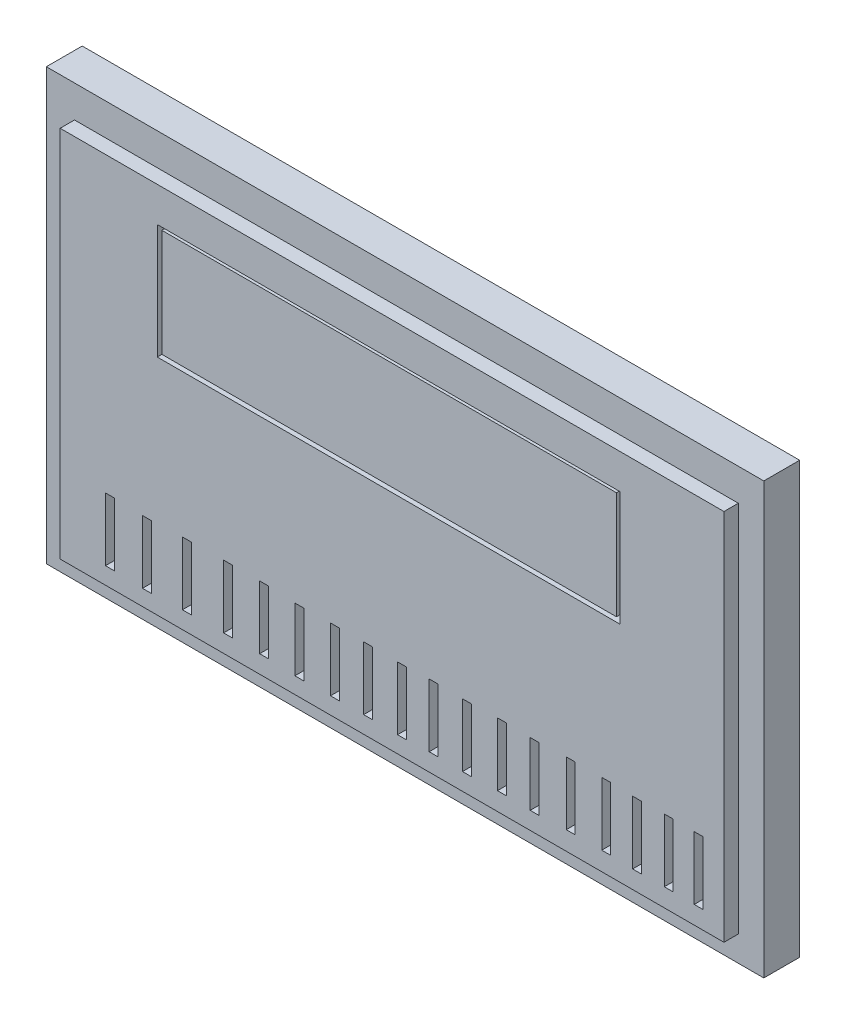
SolidWorks part; units mm, degrees
material "ABS PC"
ref_plane "Front Plane" through (0, 0, 0) normal (0, 0, 1) x (1, 0, 0)
ref_plane "Top Plane" through (0, 0, 0) normal (0, 1, 0) x (1, 0, 0)
ref_plane "Right Plane" through (0, 0, 0) normal (1, 0, 0) x (0, 0, -1)
sketch "Sketch2" plane through (0, 0, 0) normal (0, 0, 1) x (1, 0, 0)
  line L1 (-29.7872, 22.9787) -> (70.2128, 22.9787)
  line L2 (-29.7872, 22.9787) -> (-29.7872, -37.0213)
  line L3 (-29.7872, -37.0213) -> (70.2128, -37.0213)
  line L4 (70.2128, 22.9787) -> (70.2128, -37.0213)
  dimension "D1" = 100
  dimension "D2" = 60
extrude "Boss-Extrude1" add sketch "Sketch2" along normal blind 5
sketch "Sketch3" plane through (0, 0, 5) normal (0, 0, 1) x (1, 0, 0)
  line L1 (-25.8599, 18.5127) -> (66.6601, 18.5127)
  line L2 (-25.8599, 18.5127) -> (-25.8599, -33.4873)
  line L3 (-25.8599, -33.4873) -> (66.6601, -33.4873)
  line L4 (66.6601, 18.5127) -> (66.6601, -33.4873)
  dimension "D1" = 92.52
  dimension "D2" = 52
extrude "Boss-Extrude2" add sketch "Sketch3" along normal blind 2
sketch "Sketch4" plane through (0, 0, 0) normal (0, 0, -1) x (-1, 0, 0)
  line L1 (-52.1735, 13.6653) -> (12.3265, 13.6653)
  line L2 (-52.1735, 13.6653) -> (-52.1735, -2.3347)
  line L3 (-52.1735, -2.3347) -> (12.3265, -2.3347)
  line L4 (12.3265, 13.6653) -> (12.3265, -2.3347)
  dimension "D1" = 16
  dimension "D2" = 64.5
extrude "Cut-Extrude1" cut sketch "Sketch4" against normal blind 14
sketch "Sketch5" plane through (0, 0, 0) normal (0, 0, -1) x (-1, 0, 0)
  line L0 (-59.5883, -22.1519) -> (-58.3471, -22.1519)
  line L1 (-63.758, -22.1977) -> (-62.5168, -22.1977)
  line L2 (-63.758, -22.1977) -> (-63.758, -30.9895)
  line L3 (-63.758, -30.9895) -> (-62.5168, -30.9895)
  line L4 (-62.5168, -22.1977) -> (-62.5168, -30.9895)
  line L5 (-59.5883, -22.1519) -> (-59.5883, -30.9437)
  line L6 (-59.5883, -30.9437) -> (-58.3471, -30.9437)
  line L7 (-58.3471, -22.1519) -> (-58.3471, -30.9437)
  line L8 (-55.1704, -22.2108) -> (-53.9292, -22.2108)
  line L9 (-55.1704, -22.2108) -> (-55.1704, -31.0026)
  line L10 (-55.1704, -31.0026) -> (-53.9292, -31.0026)
  line L11 (-53.9292, -22.2108) -> (-53.9292, -31.0026)
  line L16 (-50.8703, -22.093) -> (-49.6291, -22.093)
  line L17 (-50.8703, -22.093) -> (-50.8703, -30.8848)
  line L18 (-50.8703, -30.8848) -> (-49.6291, -30.8848)
  line L19 (-49.6291, -22.093) -> (-49.6291, -30.8848)
  line L20 (-45.9223, -22.093) -> (-44.6811, -22.093)
  line L21 (-45.9223, -22.093) -> (-45.9223, -30.8848)
  line L22 (-45.9223, -30.8848) -> (-44.6811, -30.8848)
  line L23 (-44.6811, -22.093) -> (-44.6811, -30.8848)
  line L24 (-40.8963, -22.2716) -> (-39.6551, -22.2716)
  line L25 (-40.8963, -22.2716) -> (-40.8963, -31.0634)
  line L26 (-40.8963, -31.0634) -> (-39.6551, -31.0634)
  line L27 (-39.6551, -22.2716) -> (-39.6551, -31.0634)
  line L28 (-36.3326, -22.1765) -> (-35.0914, -22.1765)
  line L29 (-36.3326, -22.1765) -> (-36.3326, -30.9683)
  line L30 (-36.3326, -30.9683) -> (-35.0914, -30.9683)
  line L31 (-35.0914, -22.1765) -> (-35.0914, -30.9683)
  line L32 (-31.4565, -22.3097) -> (-30.2153, -22.3097)
  line L33 (-31.4565, -22.3097) -> (-31.4565, -31.1015)
  line L34 (-31.4565, -31.1015) -> (-30.2153, -31.1015)
  line L35 (-30.2153, -22.3097) -> (-30.2153, -31.1015)
  line L36 (-26.8145, -22.2395) -> (-25.5733, -22.2395)
  line L37 (-26.8145, -22.2395) -> (-26.8145, -31.0313)
  line L38 (-26.8145, -31.0313) -> (-25.5733, -31.0313)
  line L39 (-25.5733, -22.2395) -> (-25.5733, -31.0313)
  line L40 (-22.4079, -22.3852) -> (-21.1667, -22.3852)
  line L41 (-22.4079, -22.3852) -> (-22.4079, -31.177)
  line L42 (-22.4079, -31.177) -> (-21.1667, -31.177)
  line L43 (-21.1667, -22.3852) -> (-21.1667, -31.177)
  line L44 (-17.682, -22.325) -> (-16.4408, -22.325)
  line L45 (-17.682, -22.325) -> (-17.682, -31.1168)
  line L46 (-17.682, -31.1168) -> (-16.4408, -31.1168)
  line L47 (-16.4408, -22.325) -> (-16.4408, -31.1168)
  line L48 (-13.0637, -22.36) -> (-11.8225, -22.36)
  line L49 (-13.0637, -22.36) -> (-13.0637, -31.1518)
  line L50 (-13.0637, -31.1518) -> (-11.8225, -31.1518)
  line L51 (-11.8225, -22.36) -> (-11.8225, -31.1518)
  line L52 (-8.0956, -22.43) -> (-6.8544, -22.43)
  line L53 (-8.0956, -22.43) -> (-8.0956, -31.2218)
  line L54 (-8.0956, -31.2218) -> (-6.8544, -31.2218)
  line L55 (-6.8544, -22.43) -> (-6.8544, -31.2218)
  line L56 (-3.1883, -22.2201) -> (-1.9471, -22.2201)
  line L57 (-3.1883, -22.2201) -> (-3.1883, -31.0119)
  line L58 (-3.1883, -31.0119) -> (-1.9471, -31.0119)
  line L59 (-1.9471, -22.2201) -> (-1.9471, -31.0119)
  line L60 (1.8406, -22.2201) -> (3.0818, -22.2201)
  line L61 (1.8406, -22.2201) -> (1.8406, -31.0119)
  line L62 (1.8406, -31.0119) -> (3.0818, -31.0119)
  line L63 (3.0818, -22.2201) -> (3.0818, -31.0119)
  line L64 (7.5795, -22.2992) -> (8.8207, -22.2992)
  line L65 (7.5795, -22.2992) -> (7.5795, -31.091)
  line L66 (7.5795, -31.091) -> (8.8207, -31.091)
  line L67 (8.8207, -22.2992) -> (8.8207, -31.091)
extrude "Cut-Extrude2" cut sketch "Sketch5" against normal blind 14
sketch "Sketch6" plane through (0, 0, 0) normal (0, 0, -1) x (-1, 0, 0)
  line L0 (13.147, -22.4941) -> (14.3882, -22.4941)
  line L1 (13.147, -22.4941) -> (13.147, -31.2859)
  line L2 (13.147, -31.2859) -> (14.3882, -31.2859)
  line L3 (14.3882, -22.4941) -> (14.3882, -31.2859)
  line L8 (18.3076, -22.3422) -> (19.5488, -22.3422)
  line L9 (18.3076, -22.3422) -> (18.3076, -31.134)
  line L10 (18.3076, -31.134) -> (19.5488, -31.134)
  line L11 (19.5488, -22.3422) -> (19.5488, -31.134)
extrude "Cut-Extrude3" cut sketch "Sketch6" against normal blind 14
sketch "Sketch7" plane through (0, 0, 0) normal (0, 0, -1) x (-1, 0, 0)
  line L1 (-51.6783, 13.2845) -> (11.6978, 13.2845)
  line L2 (-51.6783, 13.2845) -> (-51.6783, -1.6901)
  line L3 (-51.6783, -1.6901) -> (11.6978, -1.6901)
  line L4 (11.6978, 13.2845) -> (11.6978, -1.6901)
extrude "Boss-Extrude8" add sketch "Sketch7" against normal blind 7 from offset 0 separate body
